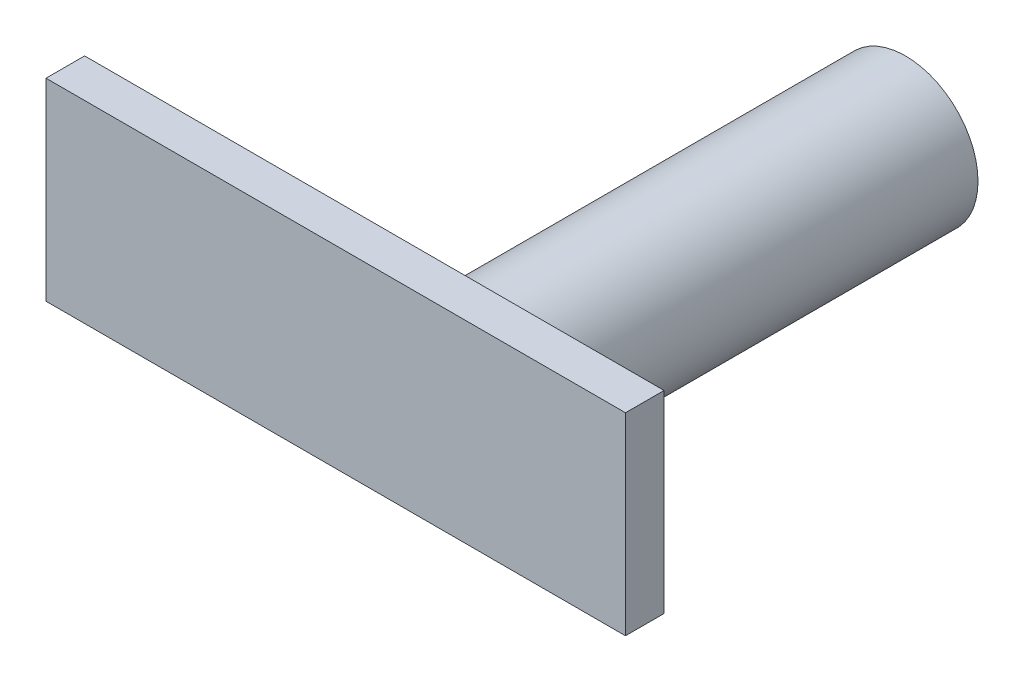
SolidWorks part; units mm, degrees
ref_plane "Front Plane" through (0, 0, 0) normal (0, 0, 1) x (1, 0, 0)
ref_plane "Top Plane" through (0, 0, 0) normal (0, 1, 0) x (1, 0, 0)
ref_plane "Right Plane" through (0, 0, 0) normal (1, 0, 0) x (0, 0, -1)
sketch "Sketch1" plane through (0, 0, 0) normal (0, 0, 1) x (1, 0, 0)
  line L1 (-10, -10) -> (10, -10)
  line L2 (-10, -10) -> (-10, 10)
  line L3 (-10, 10) -> (10, 10)
  line L4 (10, -10) -> (10, 10)
  line L5 (-10, -10) -> (10, 10) construction
  line L6 (-10, 10) -> (10, -10) construction
  point P0 (0, 0)
ref_plane "Plane1" through (0, 0, 5) normal (0, 0, 1) x (1, 0, 0)
sketch "Sketch2" plane through (0, 0, 5) normal (0, 0, 1) x (1, 0, 0)
  line L0 (-4, 4.1502) -> (-4, -4.1502)
  line L1 (-3.2572, -4.5873) -> (4.2133, -0.4371)
  line L2 (4.2133, 0.4371) -> (-3.2572, 4.5873)
  arc A0 (4.2133, -0.4371) -> (4.2133, 0.4371) centre (3.9704, 0) ccw
  arc A1 (-3.2572, -4.5873) -> (-4, -4.1502) centre (-3.5, -4.1502) cw
  arc A2 (-4, 4.1502) -> (-3.2572, 4.5873) centre (-3.5, 4.1502) cw
  dimension "D1" = 0.5
sketch "Sketch4" plane through (0, 0, 5) normal (0, 0, 1) x (1, 0, 0)
  line L1 (-4, 1) -> (2, 1)
  line L2 (-4, 1) -> (-4, -1)
  line L3 (-4, -1) -> (2, -1)
  line L4 (2, 1) -> (2, -1)
sketch "Sketch6" plane through (0, 0, 5) normal (0, 0, 1) x (1, 0, 0)
  circle A0 centre (0, 0) radius 0.5
  circle A1 centre (0, 0) radius 0.75
extrude "Boss-Extrude3" add sketch "Sketch4" along normal blind 0.4
sketch "Sketch7" plane through (0, 0, 5) normal (0, 0, 1) x (1, 0, 0)
  circle A0 centre (0, 0) radius 0.5
  circle A1 centre (0, 0) radius 0.75
extrude "Boss-Extrude4" add sketch "Sketch6" against normal blind 4.5 contours A1
sketch "Sketch8" plane through (0, 0, 0) normal (0, 0, 1) x (1, 0, 0)
  line L1 (-1, 3) -> (1, 3)
  line L2 (-1, 3) -> (-1, -3)
  line L3 (-1, -3) -> (1, -3)
  line L4 (1, 3) -> (1, -3)
